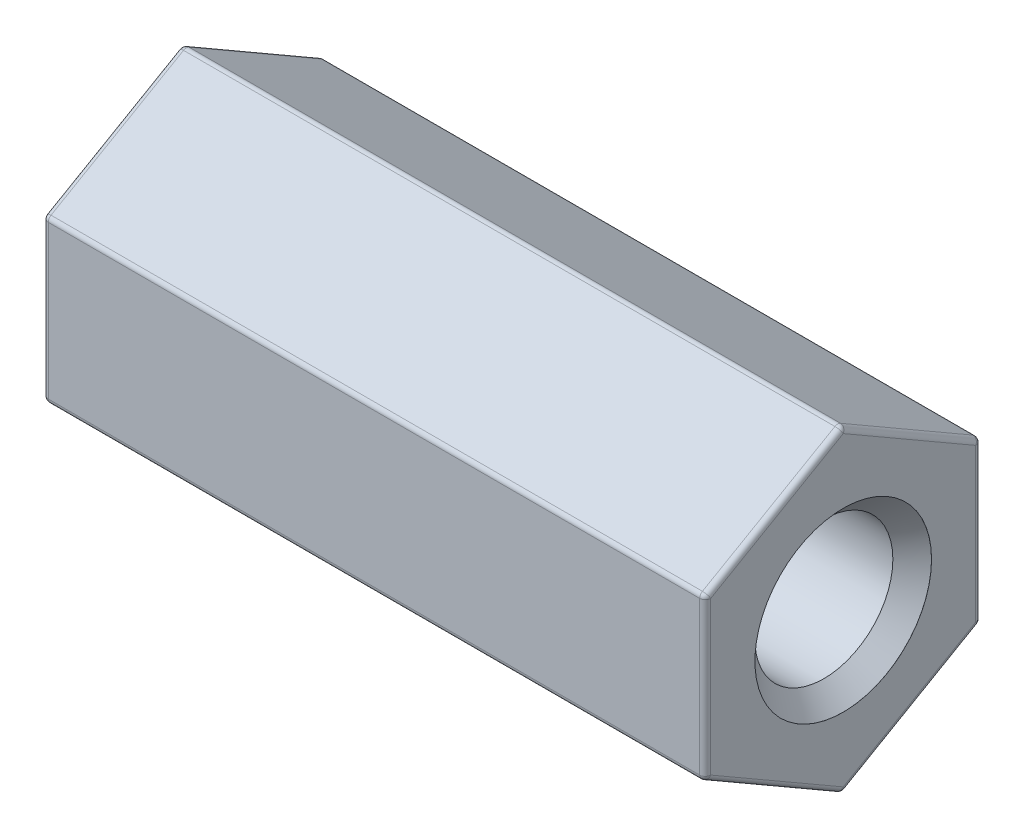
SolidWorks part; units mm, degrees
ref_plane "Front Plane" through (0, 0, 0) normal (0, 0, 1) x (1, 0, 0)
ref_plane "Top Plane" through (0, 0, 0) normal (0, 1, 0) x (1, 0, 0)
ref_plane "Right Plane" through (0, 0, 0) normal (1, 0, 0) x (0, 0, -1)
ref_plane "Plane1" through (12, 0, 0) normal (1, 0, 0) x (0, 0, -1)
sketch "Sketch1" plane through (12, 0, 0) normal (1, 0, 0) x (0, 0, -1)
  line L0 (-2.5, 1.4434) -> (-2.5, -1.4434)
  line L1 (-2.5, -1.4434) -> (0, -2.8868)
  line L2 (0, -2.8868) -> (2.5, -1.4434)
  line L3 (2.5, -1.4434) -> (2.5, 1.4434)
  line L4 (2.5, 1.4434) -> (0, 2.8868)
  line L5 (0, 2.8868) -> (-2.5, 1.4434)
  dimension "D1" = 2.5
  dimension "D2" = 5
  dimension "D3" = 1.4434
  dimension "D4" = 4.3301
  dimension "D5" = 5.7735
extrude "Boss-Extrude1" add sketch "Sketch1" against normal blind 12
sketch "Sketch2" plane through (0, 0, 0) normal (0, 0, 1) x (1, 0, 0)
  line L0 (0, 1.6) -> (0, 0)
  line L1 (0, 0) -> (12, 0)
  line L2 (12, 0) -> (12, 1.6)
  line L3 (12, 1.6) -> (11.999, 1.6)
  line L4 (11.999, 1.6) -> (11.649, 1.25)
  line L5 (11.649, 1.25) -> (0.351, 1.25)
  line L6 (0.351, 1.25) -> (0.001, 1.6)
  line L7 (0.001, 1.6) -> (0, 1.6)
  line L8 (0, 0) -> (12, 0) construction
  dimension "D1" = 0.001
  dimension "D2" = 0.351
  dimension "D3" = 11.649
  dimension "D4" = 11.999
  dimension "D5" = 12
  dimension "D6" = 1.25
  dimension "D7" = 1.6
revolve "Cut-Revolve1" cut sketch "Sketch2" angle 360 about L8
fillet "Fillet1" radius 0.1 18 edges at (12, -2.1651, -1.25) (12, 0, -2.5) (6, -1.4434, -2.5) (12, -2.1651, 1.25) (6, -2.8868, 0) (0, -2.1651, -1.25) (12, 2.1651, -1.25) (12, 2.1651, 1.25) (12, 0, 2.5) (6, 1.4434, -2.5) (0, 0, -2.5) (6, -1.4434, 2.5) (0, -2.1651, 1.25) (6, 2.8868, 0) (6, 1.4434, 2.5) (0, 2.1651, -1.25) (0, 0, 2.5) (0, 2.1651, 1.25)
